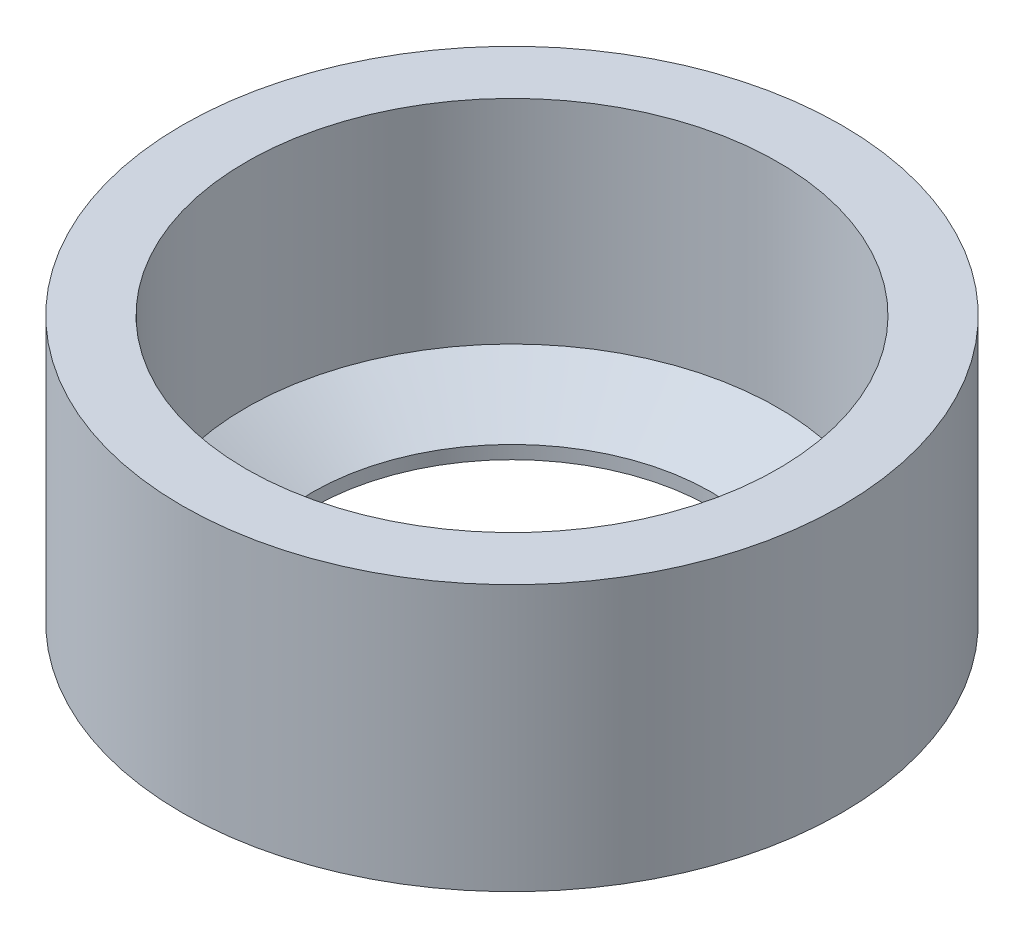
SolidWorks part; units mm, degrees
material "1023 Carbon Steel Sheet (SS)"
ref_plane "Front Plane" through (0, 0, 0) normal (0, 0, 1) x (1, 0, 0)
ref_plane "Top Plane" through (0, 0, 0) normal (0, 1, 0) x (1, 0, 0)
ref_plane "Right Plane" through (0, 0, 0) normal (1, 0, 0) x (0, 0, -1)
sketch "Sketch1" plane through (0, 0, 0) normal (0, 1, 0) x (1, 0, 0)
  circle A0 centre (0, 0) radius 15.748
  dimension "D1" = 31.496
extrude "Boss-Extrude1" add sketch "Sketch1" along normal blind 12.7
hole_wizard "1 (1) Diameter Hole1" positions "3DSketch1" profile "Sketch3" hole size "1" standard "ANSI Inch"
sketch3d "3DSketch1"
  circle A0 centre (0, 12.7, 0) radius 15.748 construction
  point P0 (0, 12.7, 0)
  point P5 (0, 28.448, 0)
sketch "Sketch3" plane through (0, 12.7, 0) normal (1, 0, 0) x (0, 0, 1)
  line L0 (0, 0) -> (0, 17.7909)
  line L1 (0, 17.7909) -> (12.7, 10.16)
  line L2 (12.7, 10.16) -> (12.7, 0)
  line L5 (12.7, 0) -> (0, 0)
  line L10 (0, 17.7909) -> (-12.7, 10.16) construction
  line L11 (0, -6.35) -> (0, 107.95) construction
  dimension "Hole Dia." = 25.4
  dimension "Hole Depth" = 10.16
  dimension "Drill Angle" = 118
hole_wizard "3/4 (0.75) Diameter Hole1" positions "3DSketch2" profile "Sketch5" hole size "3/4" standard "ANSI Inch" end condition through all
sketch3d "3DSketch2"
  circle A0 centre (0, 12.7, 0) radius 12.7 construction
  point P0 (0, 12.7, 0)
  point P5 (0, 25.4, 0)
sketch "Sketch5" plane through (0, 12.7, 0) normal (1, 0, 0) x (0, 0, 1)
  line L0 (0, 0) -> (0, 12.7)
  line L1 (0, 12.7) -> (9.525, 12.7)
  line L2 (9.525, 12.7) -> (9.525, 0)
  line L5 (9.525, 0) -> (0, 0)
  line L11 (0, -6.35) -> (0, 107.95) construction
  dimension "Thru Hole Dia." = 19.05
  dimension "Thru Hole Depth" = 12.7
